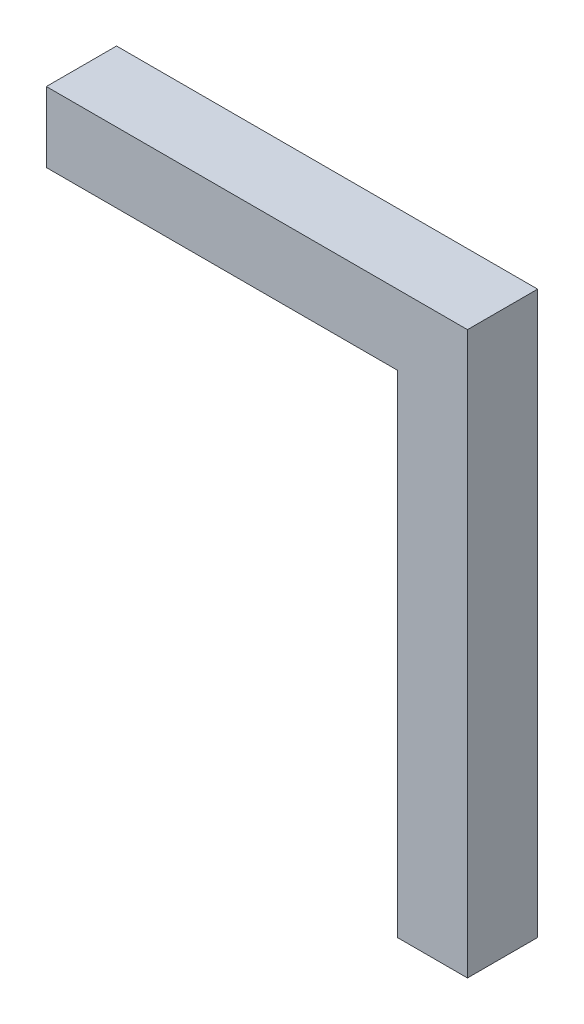
SolidWorks part; units mm, degrees
ref_plane "Front" through (0, 0, 0) normal (0, 0, 1) x (1, 0, 0)
ref_plane "Top" through (0, 0, 0) normal (0, 1, 0) x (1, 0, 0)
ref_plane "Right" through (0, 0, 0) normal (1, 0, 0) x (0, 0, -1)
sketch "Sketch1" plane through (0, 0, 0) normal (0, 0, 1) x (1, 0, 0)
  line L0 (-8.2, 17.5626) -> (-8.2, 17.0626)
  line L1 (-8.2, 17.5626) -> (-5.2, 17.5626)
  line L2 (-8.2, 17.5626) -> (-8.2, 17.0626)
  line L3 (-5.7, 13.5626) -> (-5.2, 13.5626)
  line L4 (-5.2, 17.5626) -> (-5.2, 13.5626)
  line L7 (-8.2, 17.0626) -> (-5.7, 17.0626)
  line L9 (-5.2, 13.5626) -> (-5.7, 13.5626)
  line L10 (-5.7, 13.5626) -> (-5.7, 17.0626)
  point P4 (16.4765, -3.1811)
  dimension "D1" = 0.5
  dimension "D2" = 0.5
  dimension "D3" = 4
  dimension "D4" = 3
extrude "Boss-Extrude1" add sketch "Sketch1" along normal blind 0.5 contours L10 L3 L4 L1 L0 L7
